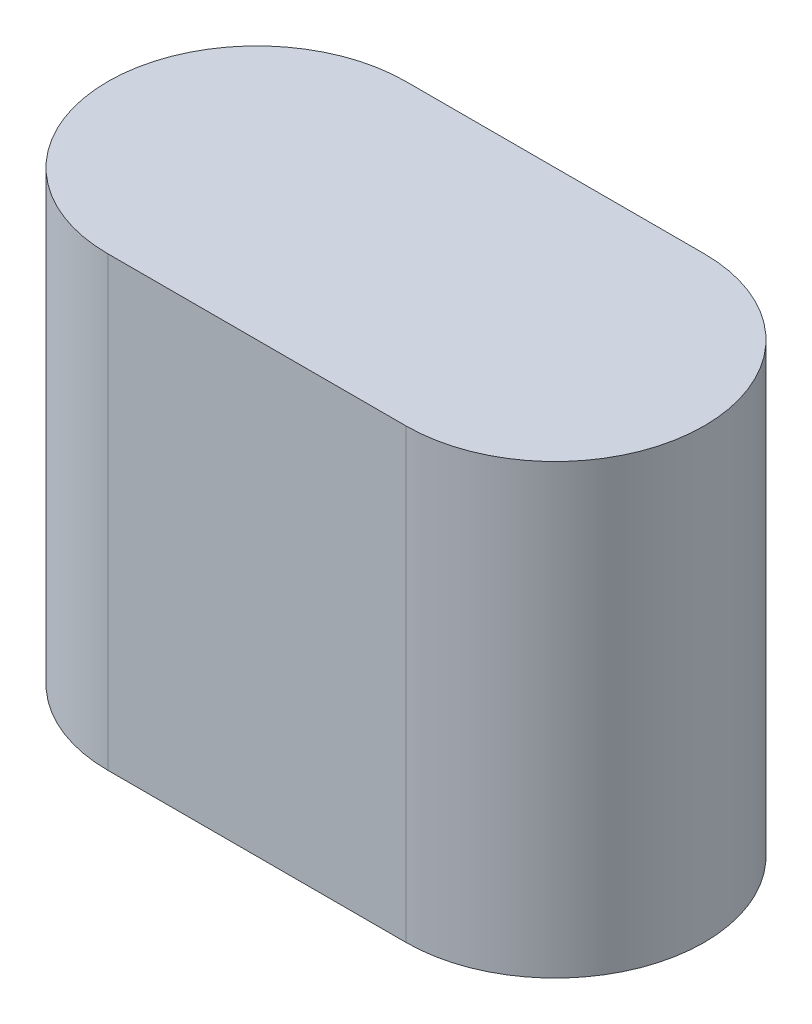
SolidWorks part; units mm, degrees
ref_plane "Front Plane" through (0, 0, 0) normal (0, 0, 1) x (1, 0, 0)
ref_plane "Top Plane" through (0, 0, 0) normal (0, 1, 0) x (1, 0, 0)
ref_plane "Right Plane" through (0, 0, 0) normal (1, 0, 0) x (0, 0, -1)
sketch "Sketch1" plane through (0, 0, 0) normal (0, 1, 0) x (1, 0, 0)
  line L0 (-2.54, 2.54) -> (2.54, 2.54)
  line L1 (2.54, -2.54) -> (-2.54, -2.54)
  line L2 (-2.54, 0) -> (2.54, 0) construction
  arc A0 (-2.54, 2.54) -> (-2.54, -2.54) centre (-2.54, 0) ccw
  arc A1 (2.54, -2.54) -> (2.54, 2.54) centre (2.54, 0) ccw
  point P1 (0, 0)
  dimension "D1" = 2.54
  dimension "D2" = 5.08
extrude "Extrude1" add sketch "Sketch1" along normal blind 7.62
